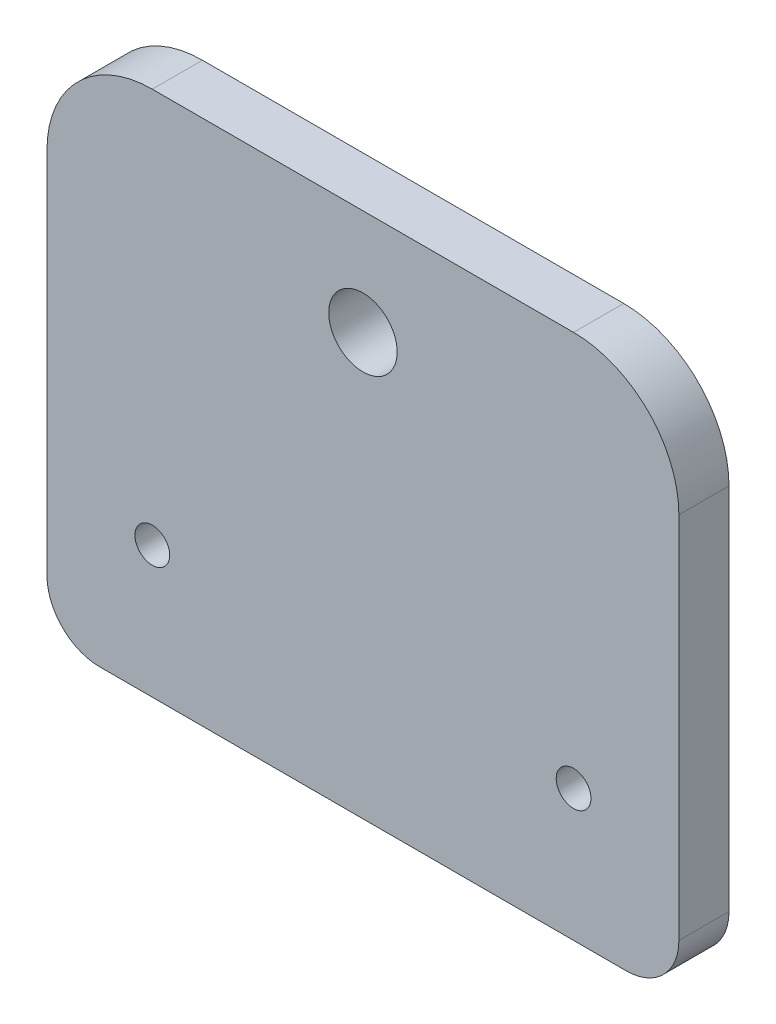
SolidWorks part; units mm, degrees
ref_plane "Front Plane" through (0, 0, 0) normal (0, 0, 1) x (1, 0, 0)
ref_plane "Top Plane" through (0, 0, 0) normal (0, 1, 0) x (1, 0, 0)
ref_plane "Right Plane" through (0, 0, 0) normal (1, 0, 0) x (0, 0, -1)
sketch "Sketch1" plane through (0, 0, 0) normal (0, 0, 1) x (1, 0, 0)
  line L1 (0, 0) -> (60, 0)
  line L2 (0, 0) -> (0, 50)
  line L3 (0, 50) -> (60, 50)
  line L4 (60, 0) -> (60, 50)
  dimension "D1" = 50
  dimension "D2" = 60
extrude "Boss-Extrude1" add sketch "Sketch1" along normal blind 4.76
sketch "Sketch2" plane through (0, 0, 4.76) normal (0, 0, 1) x (1, 0, 0)
  line L0 (0, 12.5) -> (60, 12.5) construction
  line L1 (0, 50) -> (0, 0) construction
  line L2 (60, 0) -> (60, 50) construction
  line L3 (0, 0) -> (60, 0) construction
  line L4 (30, 50) -> (30, 0) construction
  line L5 (60, 50) -> (0, 50) construction
  circle A0 centre (10, 12.5) radius 1.65
  circle A2 centre (50, 12.5) radius 1.65
  circle A3 centre (30, 40) radius 3.25
  dimension "D2" = 3.3
  dimension "D4" = 6.5
  dimension "D1" = 12.5
  dimension "D3" = 20
  dimension "D5" = 10
extrude "Cut-Extrude1" cut sketch "Sketch2" against normal through all
fillet "Fillet1" radius 10 2 edges at (60, 50, 2.38) (0, 50, 2.38)
fillet "Fillet2" radius 5 2 edges at (60, 0, 2.38) (0, 0, 2.38)
equation "\"Screw Size\" = 6mm"
equation "\"D4@Sketch2\"= \"Screw Size\" + 0.5mm"
